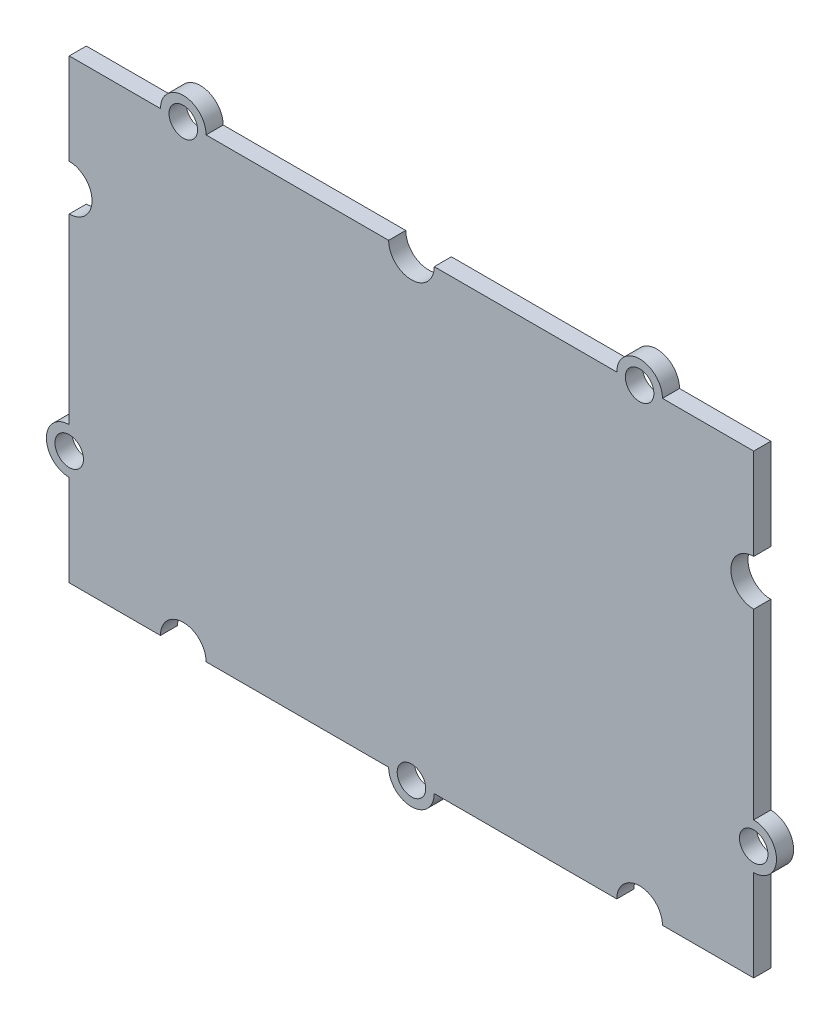
SolidWorks part; units mm, degrees
ref_plane "Plan de face" through (0, 0, 0) normal (0, 0, 1) x (1, 0, 0)
ref_plane "Plan de dessus" through (0, 0, 0) normal (0, 1, 0) x (1, 0, 0)
ref_plane "Plan de droite" through (0, 0, 0) normal (1, 0, 0) x (0, 0, -1)
sketch "Esquisse1" plane through (0, 0, 0) normal (0, 0, 1) x (1, 0, 0)
  line L0 (-33.6986, 0) -> (47.6713, 0) construction
  line L1 (0, -30.5848) -> (0, 27.1707) construction
  line L2 (-20, 27.1707) -> (-20, -30.5848) construction
  line L3 (-30, 20) -> (-22, 20)
  line L4 (-30, 20) -> (-30, 12)
  line L5 (-30, -20) -> (-22, -20)
  line L6 (30, 20) -> (30, 12)
  line L7 (20, 27.1707) -> (20, -30.5848) construction
  line L8 (-38.2508, 10) -> (36.2909, 10) construction
  line L9 (-38.2508, -10) -> (36.2909, -10) construction
  line L10 (-30, 8) -> (-30, -8)
  line L11 (-18, 20) -> (-2, 20)
  line L12 (2, 20) -> (18, 20)
  line L13 (22, 20) -> (30, 20)
  line L14 (30, 8) -> (30, -8)
  line L15 (30, -12) -> (30, -20)
  line L16 (22, -20) -> (30, -20)
  line L17 (-18, -20) -> (-2, -20)
  line L18 (-30, -12) -> (-30, -20)
  line L19 (2, -20) -> (18, -20)
  arc A0 (-18, 20) -> (-22, 20) centre (-20, 20) ccw
  arc A1 (-2, 20) -> (2, 20) centre (0, 20) ccw
  arc A2 (22, 20) -> (18, 20) centre (20, 20) ccw
  arc A3 (-30, 8) -> (-30, 12) centre (-30, 10) ccw
  arc A4 (-30, -8) -> (-30, -12) centre (-30, -10) ccw
  arc A5 (-18, -20) -> (-22, -20) centre (-20, -20) ccw
  arc A6 (-2, -20) -> (2, -20) centre (0, -20) ccw
  arc A7 (22, -20) -> (18, -20) centre (20, -20) ccw
  arc A8 (30, 12) -> (30, 8) centre (30, 10) ccw
  arc A9 (30, -12) -> (30, -8) centre (30, -10) ccw
  circle A10 centre (-20, 20) radius 1.25
  circle A11 centre (20, 20) radius 1.25
  circle A12 centre (30, -10) radius 1.25
  circle A13 centre (0, -20) radius 1.25
  circle A14 centre (-30, -10) radius 1.25
  dimension "D7" = 4
  dimension "D8" = 4
  dimension "D9" = 4
  dimension "D10" = 4
  dimension "D11" = 4
  dimension "D12" = 4
  dimension "D13" = 4
  dimension "D14" = 4
  dimension "D15" = 4
  dimension "D16" = 4
  dimension "D17" = 2.5
  dimension "D18" = 2.5
  dimension "D19" = 2.5
  dimension "D20" = 2.5
  dimension "D21" = 2.5
  dimension "D1" = 60
  dimension "D2" = 40
  dimension "D3" = 10
  dimension "D4" = 10
  dimension "D5" = 10
  dimension "D6" = 10
extrude "Boss.-Extru.1" add sketch "Esquisse1" along normal blind 1.5
